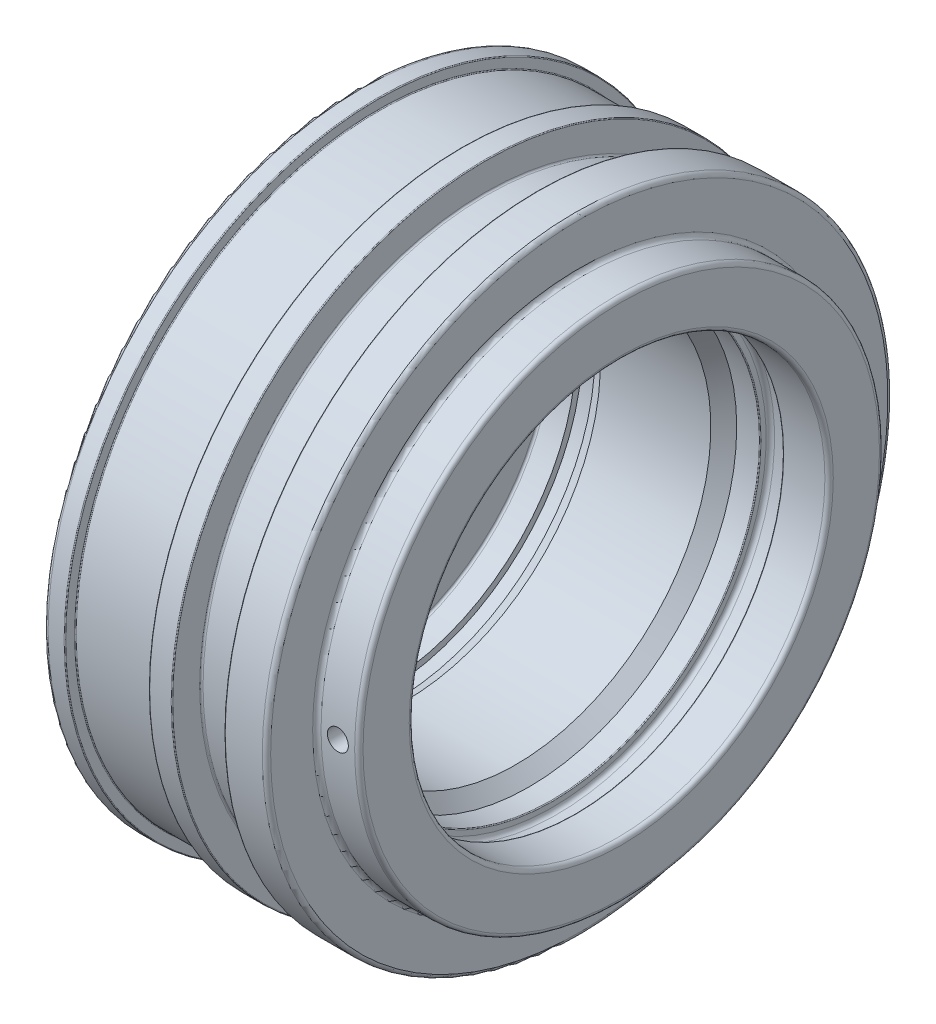
SolidWorks part; units mm, degrees
ref_plane "Front" through (0, 0, 0) normal (0, 0, 1) x (1, 0, 0)
ref_plane "Top" through (0, 0, 0) normal (0, 1, 0) x (1, 0, 0)
ref_plane "Right" through (0, 0, 0) normal (1, 0, 0) x (0, 0, -1)
sketch "Sketch1" plane through (0, 0, 0) normal (0, 0, 1) x (1, 0, 0)
  line L0 (-64.5198, 0) -> (220.5612, 0) construction
  line L1 (15, 62.5206) -> (15, 73.5)
  line L2 (16, 74.5) -> (19.8, 74.5)
  line L3 (45.5, 74.3) -> (45.5, 67.9)
  line L4 (45.9, 67.5) -> (57.6, 67.5)
  line L5 (20, 74.3) -> (20, 72.2)
  line L6 (20.2, 72) -> (39.8, 72)
  line L7 (40, 72.2) -> (40, 74.3)
  line L8 (58, 67.9) -> (58, 74.3)
  line L9 (58.2, 74.5) -> (67, 74.5)
  line L10 (40.2, 74.5) -> (45.3, 74.5)
  line L11 (26.6152, 46.4175) -> (24, 47.75)
  line L12 (52.9175, 46.4175) -> (26.6152, 46.4175)
  line L13 (68, 73.5) -> (68, 63.5)
  line L14 (14.5736, 61.7014) -> (0, 51.4969)
  line L15 (0, 51.4969) -> (0, 0)
  line L16 (52.9175, 46.4175) -> (56, 49.5)
  line L17 (56, 49.5) -> (61.4, 49.5)
  line L18 (24, 47.75) -> (21, 47.75)
  line L19 (21, 47.75) -> (21, 46.25)
  line L20 (69, 62.5) -> (77, 62.5)
  line L21 (78, 61.5) -> (78, 50.5)
  line L22 (61.6, 49.7) -> (61.6, 50.9)
  line L23 (62.6, 51.9) -> (66, 51.9)
  line L24 (67, 50.9) -> (67, 49.7)
  line L25 (21, 46.25) -> (15.5, 46.25)
  line L26 (15, 45.75) -> (15, 32.5)
  line L27 (15, 32.5) -> (20, 18.7626)
  line L28 (20, 0) -> (0, 0)
  line L29 (20, 18.7626) -> (20, 0)
  line L30 (67.2, 49.5) -> (77, 49.5)
  arc A0 (19.8, 74.5) -> (20, 74.3) centre (19.8, 74.3) cw
  arc A1 (40.2, 74.5) -> (40, 74.3) centre (40.2, 74.3) ccw
  arc A2 (20, 72.2) -> (20.2, 72) centre (20.2, 72.2) ccw
  arc A3 (39.8, 72) -> (40, 72.2) centre (39.8, 72.2) ccw
  arc A4 (45.5, 74.3) -> (45.3, 74.5) centre (45.3, 74.3) ccw
  arc A5 (58, 74.3) -> (58.2, 74.5) centre (58.2, 74.3) cw
  arc A6 (45.5, 67.9) -> (45.9, 67.5) centre (45.9, 67.9) ccw
  arc A7 (57.6, 67.5) -> (58, 67.9) centre (57.6, 67.9) ccw
  arc A8 (77, 49.5) -> (78, 50.5) centre (77, 50.5) ccw
  arc A9 (15.5, 46.25) -> (15, 45.75) centre (15.5, 45.75) ccw
  arc A10 (77, 62.5) -> (78, 61.5) centre (77, 61.5) cw
  arc A11 (69, 62.5) -> (68, 63.5) centre (69, 63.5) cw
  arc A12 (15, 73.5) -> (16, 74.5) centre (16, 73.5) cw
  arc A13 (67, 74.5) -> (68, 73.5) centre (67, 73.5) cw
  arc A14 (61.6, 50.9) -> (62.6, 51.9) centre (62.6, 50.9) cw
  arc A15 (66, 51.9) -> (67, 50.9) centre (66, 50.9) cw
  arc A16 (67, 49.7) -> (67.2, 49.5) centre (67.2, 49.7) ccw
  arc A17 (61.6, 49.7) -> (61.4, 49.5) centre (61.4, 49.7) cw
  arc A18 (14.5736, 61.7014) -> (15, 62.5206) centre (14, 62.5206) ccw
  point P34 (58, 74.5)
  point P67 (67, 49.5)
  point P73 (15, 62)
  dimension "D15" = 0.2
  dimension "D16" = 0.2
  dimension "D22" = 22
  dimension "D27" = 0.5
  dimension "D23" = 1
  dimension "D30" = 1
  dimension "D31" = 1
  dimension "D35" = 1
  dimension "D36" = 0.2
  dimension "D41" = 0.2
  dimension "D42" = 0.4
  dimension "D43" = 1
  dimension "D1" = 5
  dimension "D3" = 20
  dimension "D4" = 15
  dimension "D5" = 20
  dimension "D6" = 99
  dimension "D7" = 45
  dimension "D8" = 95.5
  dimension "D9" = 92.5
  dimension "D10" = 92.835
  dimension "D11" = 65
  dimension "D12" = 20
  dimension "D13" = 6
  dimension "D14" = 144
  dimension "D17" = 124
  dimension "D18" = 149
  dimension "D19" = 30.5
  dimension "D20" = 10
  dimension "D21" = 55
  dimension "D24" = 27
  dimension "D25" = 53
  dimension "D26" = 3
  dimension "D28" = 78
  dimension "D29" = 125
  dimension "D32" = 11
  dimension "D33" = 5.4
  dimension "D34" = 2.4
  dimension "D37" = 63
  dimension "D38" = 103.8
  dimension "D39" = 12.5
  dimension "D40" = 135
revolve "Base-Revolve" add sketch "Sketch1" angle 360 about L0
cosmetic thread "Cosmetic Thread3" parameters "D2"=95
sketch "Sketch2" plane through (0, 0, 0) normal (0, 0, 1) x (1, 0, 0)
  line L0 (0, 0) -> (78, 0) construction
  line L1 (78, -62.5) -> (78, 62.5) construction
  circle A0 centre (73, 0) radius 2.5
  dimension "D2" = 5
  dimension "D1" = 5
extrude "M6 gevindhul" cut sketch "Sketch2" along normal through all
cosmetic thread "Cosmetic Thread2" parameters "D2"=6
